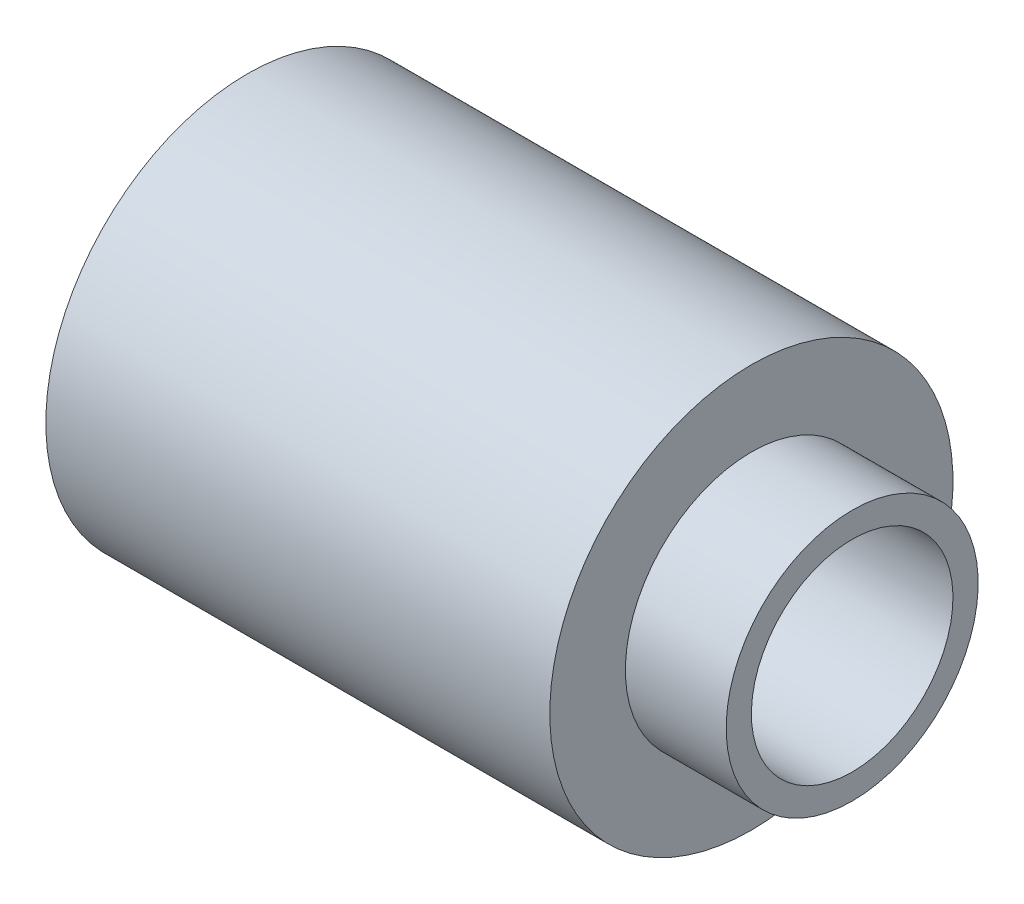
SolidWorks part; units mm, degrees
ref_plane "Front Plane" through (0, 0, 0) normal (0, 0, 1) x (1, 0, 0)
ref_plane "Top Plane" through (0, 0, 0) normal (0, 1, 0) x (1, 0, 0)
ref_plane "Right Plane" through (0, 0, 0) normal (1, 0, 0) x (0, 0, -1)
sketch "Sketch1" plane through (0, 0, 0) normal (0, 0, 1) x (1, 0, 0)
  line L0 (-6.1942, 0) -> (10.0099, 0) construction
  line L1 (-4.3761, 2) -> (-4.3761, 4)
  line L2 (-4.3761, 4) -> (5.6239, 4)
  line L3 (5.6239, 4) -> (5.6239, 2.5)
  line L4 (5.6239, 2.5) -> (7.6239, 2.5)
  line L5 (7.6239, 2.5) -> (7.6239, 2)
  line L6 (7.6239, 2) -> (-4.3761, 2)
  dimension "D1" = 2
  dimension "D2" = 2.5
  dimension "D3" = 4
  dimension "D4" = 2
  dimension "D5" = 10
revolve "Revolve1" add sketch "Sketch1" angle 360 about L0
